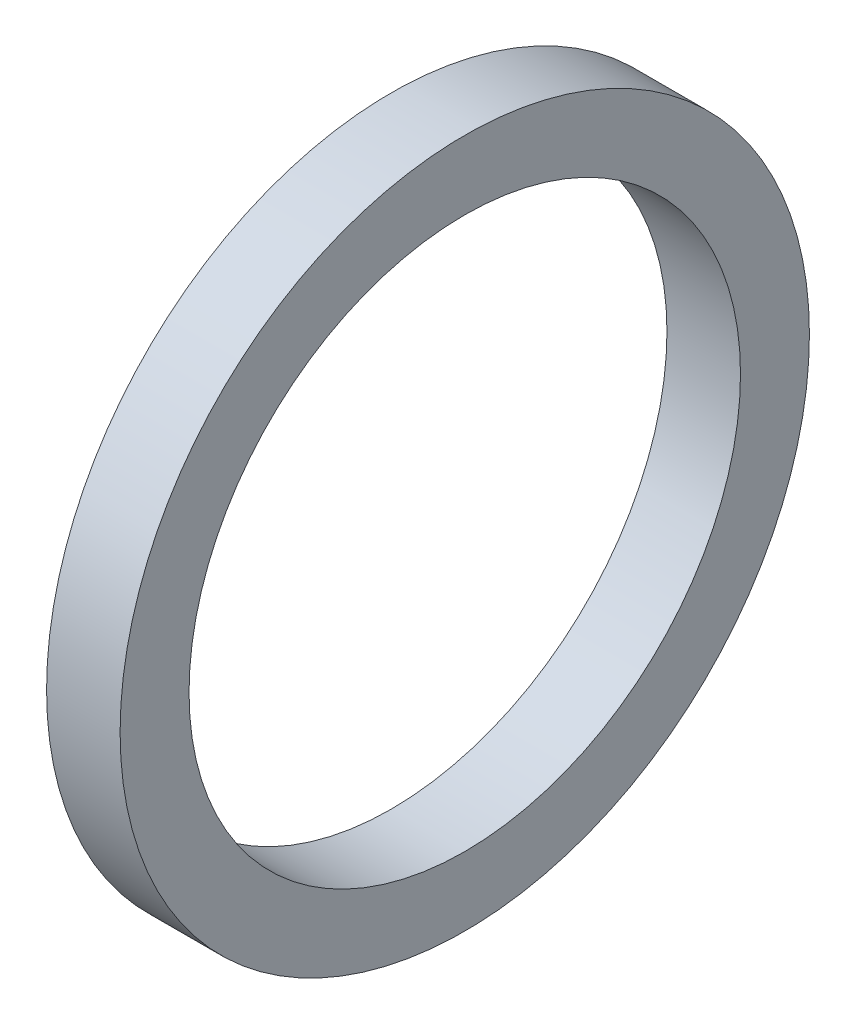
SolidWorks part; units mm, degrees
ref_plane "Front Plane" through (0, 0, 0) normal (0, 0, 1) x (1, 0, 0)
ref_plane "Top Plane" through (0, 0, 0) normal (0, 1, 0) x (1, 0, 0)
ref_plane "Right Plane" through (0, 0, 0) normal (1, 0, 0) x (0, 0, -1)
sketch "Sketch1" plane through (0, 0, 0) normal (0, 0, 1) x (1, 0, 0)
  line L0 (-43.7166, 0) -> (79.6876, 0) construction
  line L2 (0, -7.62) -> (2.032, -7.62)
  line L3 (0, -7.62) -> (0, -9.525)
  line L4 (0, -9.525) -> (2.032, -9.525)
  line L5 (2.032, -7.62) -> (2.032, -9.525)
  dimension "A" = 15.24
  dimension "B" = 19.05
  dimension "C" = 2.032
revolve "Revolve1" add sketch "Sketch1" angle 360 about L0
sketch "Sketch2" [suppressed] plane through (0, 0, 0) normal (0, 0, 1) x (1, 0, 0)
  line L0 (-34.685, 0) -> (47.6686, 0) construction
  circle A0 centre (2.54, -5.715) radius 0.762
  dimension "D1" = 2.54
  dimension "E" = 1.524
  dimension "D" = 11.938
revolve "Revolve3" [suppressed] add sketch "Sketch2" angle 360 about L0
